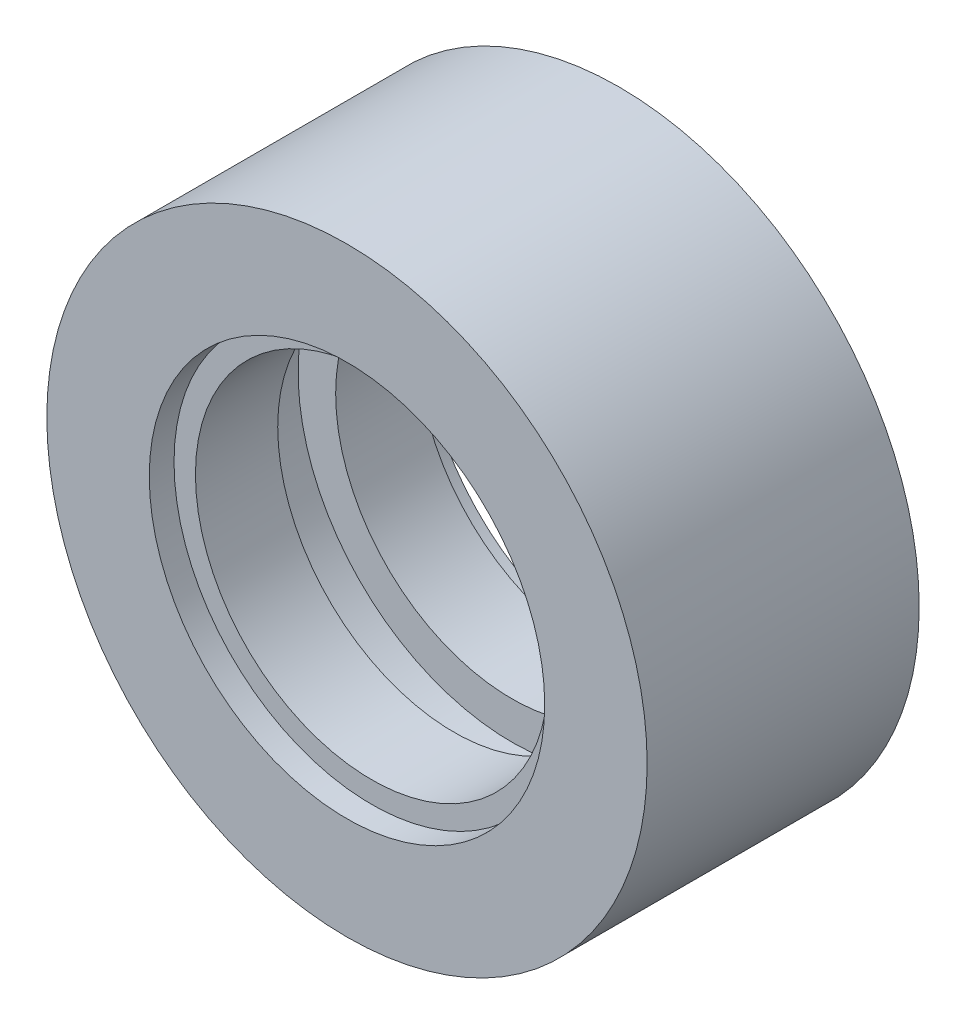
SolidWorks part; units mm, degrees
ref_plane "Płaszczyzna przednia" through (0, 0, 0) normal (0, 0, 1) x (1, 0, 0)
ref_plane "Płaszczyzna górna" through (0, 0, 0) normal (0, 1, 0) x (1, 0, 0)
ref_plane "Płaszczyzna prawa" through (0, 0, 0) normal (1, 0, 0) x (0, 0, -1)
sketch "Szkic1" plane through (0, 0, 0) normal (0, 0, 1) x (1, 0, 0)
  circle A0 centre (0, 0) radius 14.3
extrude "Dodanie-wyciągnięcie1" add sketch "Szkic1" along normal blind 12.96
sketch "Szkic2" plane through (0, 0, 12.96) normal (0, 0, 1) x (1, 0, 0)
  circle A0 centre (0, 0) radius 8.4
extrude "Wytnij-wyciągnięcie1" cut sketch "Szkic2" against normal up to next
sketch "Szkic3" plane through (0, 0, 12.96) normal (0, 0, 1) x (1, 0, 0)
  circle A0 centre (0, 0) radius 9.42
extrude "Wytnij-wyciągnięcie2" cut sketch "Szkic3" against normal blind 1.18
ref_plane "Płaszczyzna1" through (0, 0, 6.48) normal (0, 0, 1) x (1, 0, 0)
mirror "Lustro1" about plane through (0, 0, 6.48) normal (0, 0, 1) of "Wytnij-wyciągnięcie2"
sketch "Szkic5" plane through (0, 0, 6.48) normal (0, 0, 1) x (1, 0, 0)
  circle A0 centre (0, 0) radius 10.19
extrude "Wytnij-wyciągnięcie3" cut sketch "Szkic5" against normal mid plane 2.76
